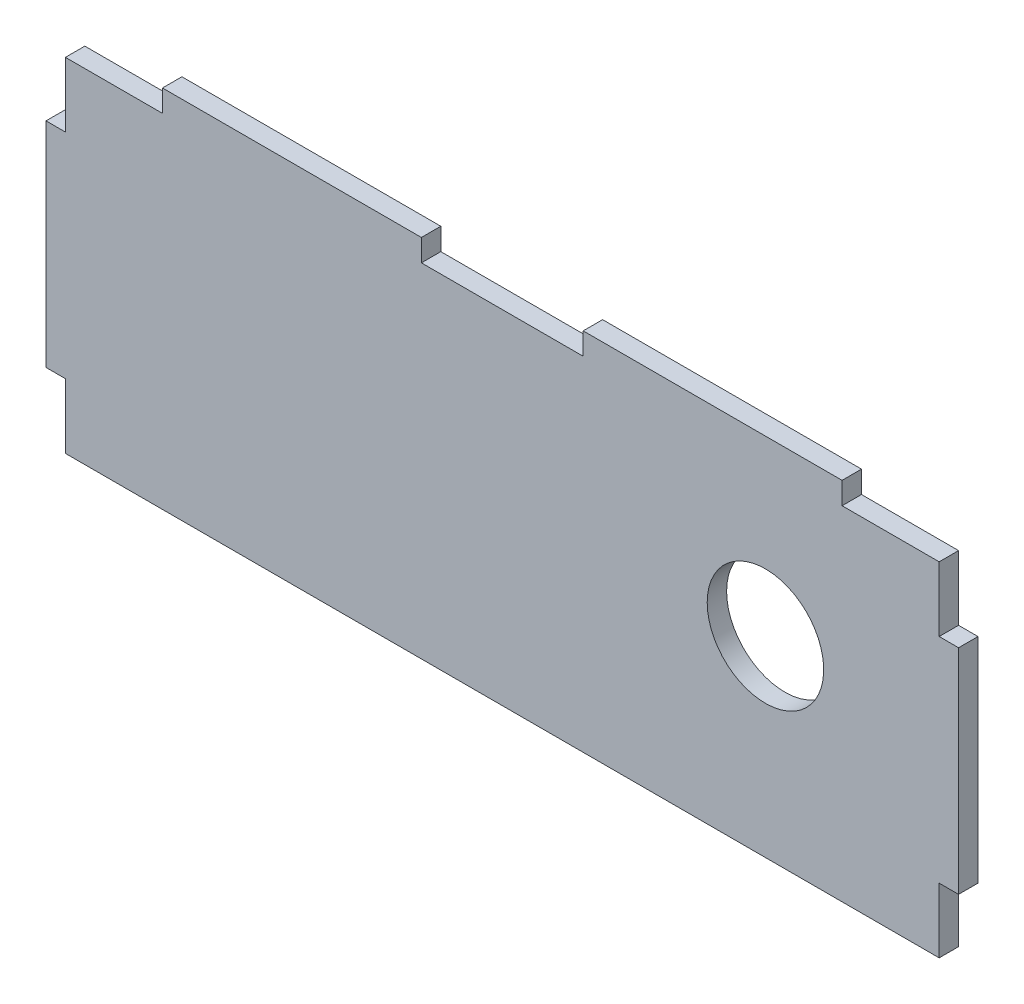
SolidWorks part; units mm, degrees
ref_plane "Plan de face" through (0, 0, 0) normal (0, 0, 1) x (1, 0, 0)
ref_plane "Plan de dessus" through (0, 0, 0) normal (0, 1, 0) x (1, 0, 0)
ref_plane "Plan de droite" through (0, 0, 0) normal (1, 0, 0) x (0, 0, -1)
sketch "Esquisse1" plane through (0, 0, 0) normal (0, 0, 1) x (1, 0, 0)
  line L1 (26.4374, -18.5355) -> (-108.5626, -18.5355)
  line L2 (26.4374, -18.5355) -> (26.4374, -71.5355)
  line L3 (26.4374, -71.5355) -> (-108.5626, -71.5355)
  line L4 (-108.5626, -18.5355) -> (-108.5626, -71.5355)
extrude "Boss.-Extru.1" add sketch "Esquisse1" along normal blind 3
sketch "Esquisse2" plane through (0, 0, 0) normal (0, 0, -1) x (-1, 0, 0)
  circle A0 centre (0.4037, -41.8992) radius 9 construction
  circle A1 centre (0.4037, -41.8992) radius 9
extrude "Enlèv. mat.-Extru.1" cut sketch "Esquisse2" against normal through all
sketch "Esquisse3" plane through (26.4374, 0, 0) normal (1, 0, 0) x (0, 0, -1)
  line L0 (0, -71.5355) -> (0, -18.5355) construction
  line L1 (0, -28.5355) -> (-3, -28.5355)
  line L2 (0, -28.5355) -> (0, -61.5355)
  line L3 (0, -61.5355) -> (-3, -61.5355)
  line L4 (-3, -28.5355) -> (-3, -61.5355)
  line L5 (-3, -71.5355) -> (-3, -18.5355) construction
  line L6 (-3, -71.5355) -> (0, -71.5355) construction
  line L7 (-3, -18.5355) -> (0, -18.5355) construction
  dimension "D1" = 10
  dimension "D2" = 10
extrude "Boss.-Extru.2" add sketch "Esquisse3" along normal up to surface (3 mm away)
sketch "Esquisse4" plane through (-108.5626, 0, 0) normal (-1, 0, 0) x (0, 0, 1)
  line L1 (0, -61.5355) -> (3, -61.5355)
  line L2 (0, -61.5355) -> (0, -28.5355)
  line L3 (0, -28.5355) -> (3, -28.5355)
  line L4 (3, -61.5355) -> (3, -28.5355)
extrude "Boss.-Extru.3" add sketch "Esquisse4" along normal up to surface (3 mm away)
sketch "Esquisse5" plane through (0, -18.5355, 0) normal (0, 1, 0) x (1, 0, 0)
  line L0 (26.4374, 0) -> (-108.5626, 0) construction
  line L1 (-93.5626, 0) -> (-53.5626, 0)
  line L2 (-93.5626, 0) -> (-93.5626, -3)
  line L3 (-93.5626, -3) -> (-53.5626, -3)
  line L4 (-53.5626, 0) -> (-53.5626, -3)
  line L5 (26.4374, -3) -> (-108.5626, -3) construction
  line L6 (-108.5626, -3) -> (-108.5626, 0) construction
  dimension "D1" = 40
  dimension "D2" = 15
extrude "Boss.-Extru.4" add sketch "Esquisse5" along normal up to surface (3.4 mm away)
sketch "Esquisse6" plane through (0, -18.5355, 0) normal (0, 1, 0) x (1, 0, 0)
  line L0 (26.4374, 0) -> (-53.5626, 0) construction
  line L1 (-28.5626, 0) -> (11.4374, 0)
  line L2 (-28.5626, 0) -> (-28.5626, -3)
  line L3 (-28.5626, -3) -> (11.4374, -3)
  line L4 (11.4374, 0) -> (11.4374, -3)
  line L5 (26.4374, -3) -> (-53.5626, -3) construction
  line L6 (26.4374, -3) -> (26.4374, 0) construction
  dimension "D1" = 40
  dimension "D2" = 15
extrude "Boss.-Extru.5" add sketch "Esquisse6" along normal up to surface (3.4 mm away)
